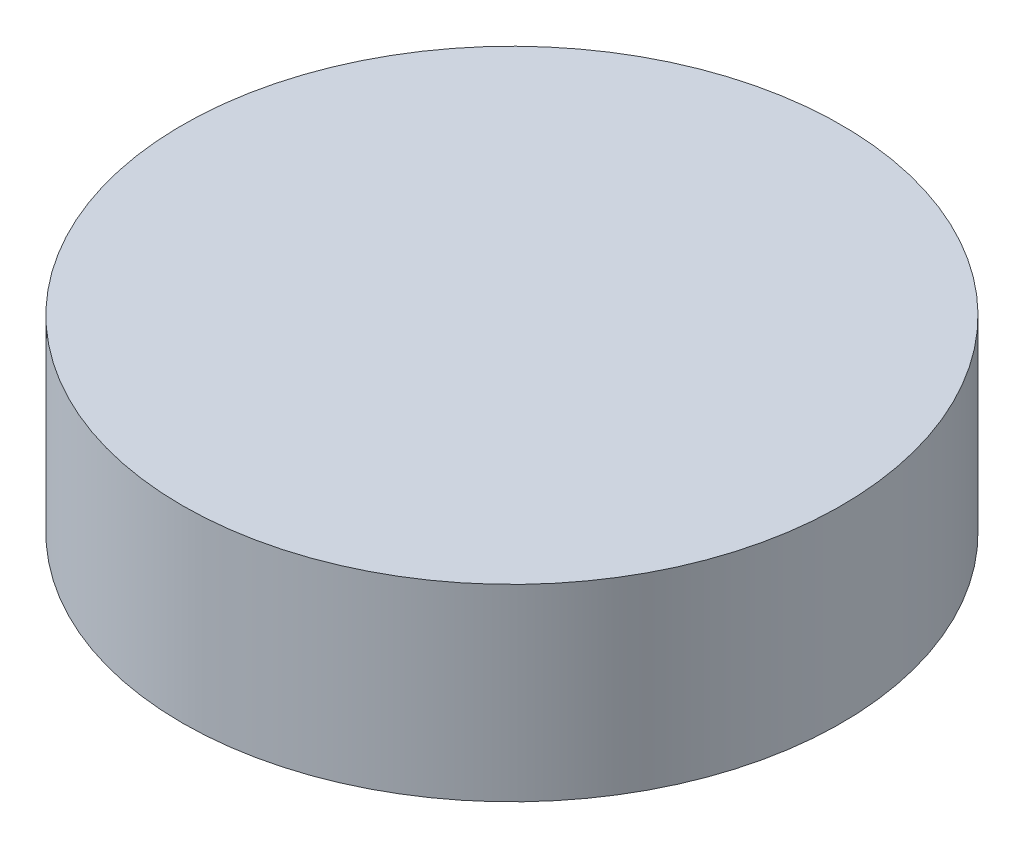
SolidWorks part; units mm, degrees
ref_plane "前视基准面" through (0, 0, 0) normal (0, 0, 1) x (1, 0, 0)
ref_plane "上视基准面" through (0, 0, 0) normal (0, 1, 0) x (1, 0, 0)
ref_plane "右视基准面" through (0, 0, 0) normal (1, 0, 0) x (0, 0, -1)
sketch "草图1" plane through (0, 0, 0) normal (0, 1, 0) x (1, 0, 0)
  circle A0 centre (0, 0) radius 17.5
  dimension "D1" = 35
extrude "凸台-拉伸1" add sketch "草图1" along normal blind 10
ref_plane "基准面1" through (0, 5, 0) normal (0, 1, 0) x (1, 0, 0)
